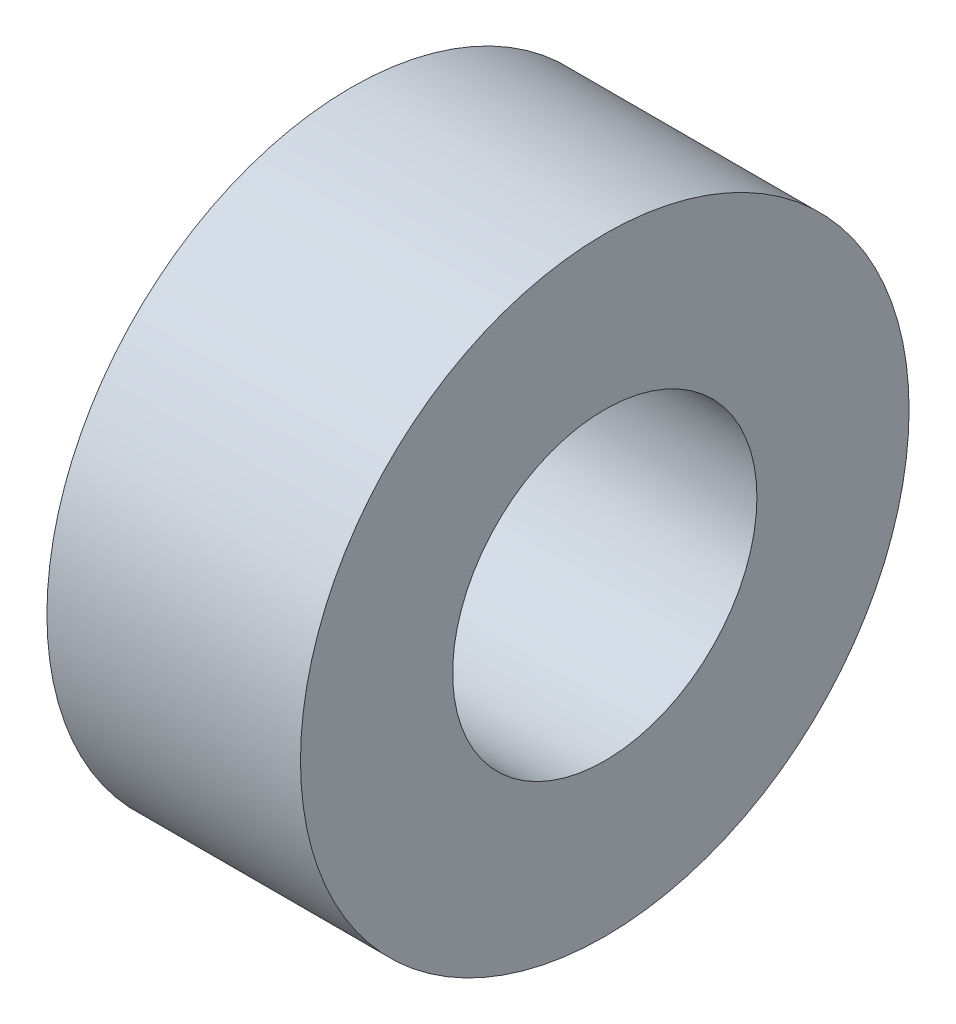
SolidWorks part; units mm, degrees
material "Chrome Stainless Steel"
ref_plane "Front Plane" through (0, 0, 0) normal (0, 0, 1) x (1, 0, 0)
ref_plane "Top Plane" through (0, 0, 0) normal (0, 1, 0) x (1, 0, 0)
ref_plane "Right Plane" through (0, 0, 0) normal (1, 0, 0) x (0, 0, -1)
sketch "Sketch1" plane through (0, 0, 0) normal (0, 0, -1) x (-1, 0, 0)
  line L0 (-2.8957, 0) -> (3.6977, 0) construction
  line L1 (-1.25, 3) -> (1.25, 3)
  line L2 (-1.25, 3) -> (-1.25, 1.5)
  line L3 (-1.25, 1.5) -> (1.25, 1.5)
  line L4 (1.25, 3) -> (1.25, 1.5)
  point P7 (0, 1.5)
  dimension "D1" = 2.5
  dimension "D2" = 1.5
  dimension "D3" = 3
revolve "Revolve1" add sketch "Sketch1" angle 360 about L0
